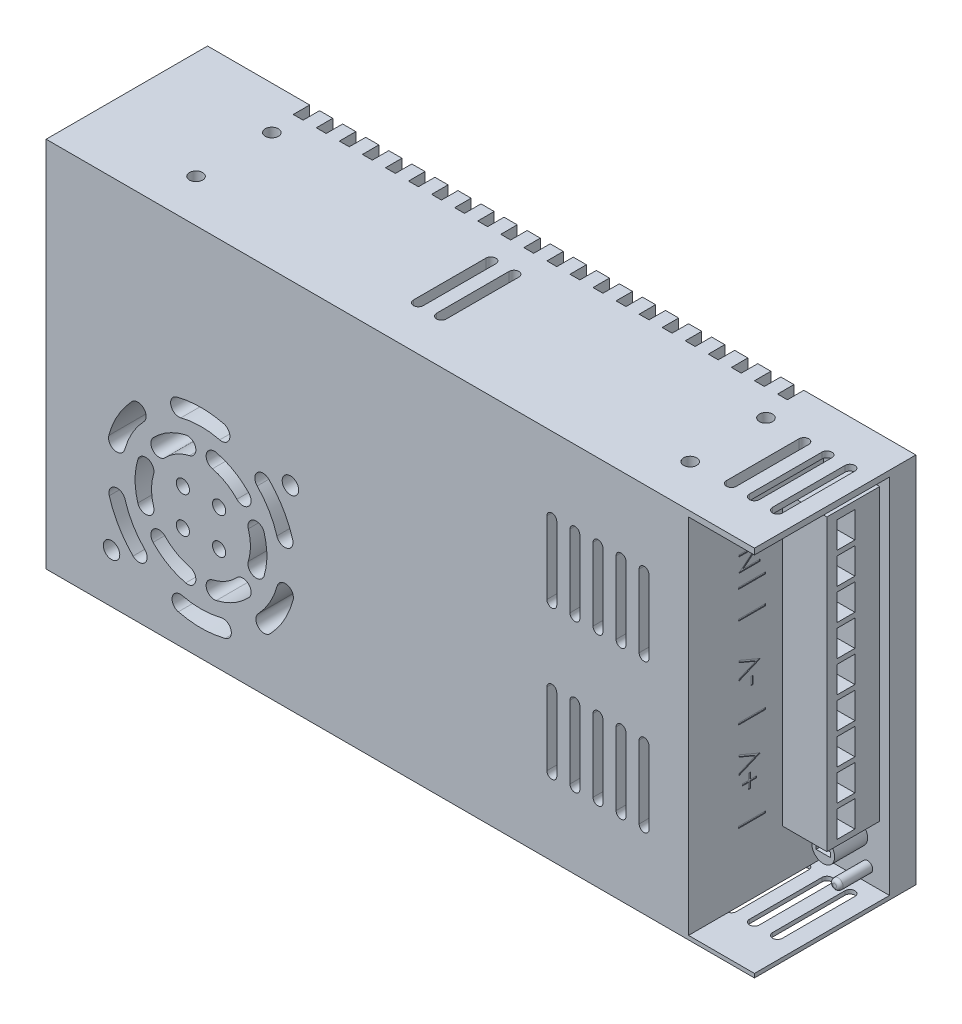
SolidWorks part; units mm, degrees
material "5454-H111"
ref_plane "Front" through (0, 0, 0) normal (0, 0, 1) x (1, 0, 0)
ref_plane "Top" through (0, 0, 0) normal (0, 1, 0) x (1, 0, 0)
ref_plane "Right" through (0, 0, 0) normal (1, 0, 0) x (0, 0, -1)
sketch "Sketch1" plane through (0, 0, 0) normal (0, 0, 1) x (1, 0, 0)
  line L1 (107.5, -56.5) -> (-107.5, -56.5)
  line L2 (107.5, -56.5) -> (107.5, 56.5)
  line L3 (107.5, 56.5) -> (-107.5, 56.5)
  line L4 (-107.5, -56.5) -> (-107.5, 56.5)
  line L5 (107.5, -56.5) -> (-107.5, 56.5) construction
  line L6 (107.5, 56.5) -> (-107.5, -56.5) construction
  point P0 (0, 0)
  dimension "D1" = 113
  dimension "D2" = 215
extrude "Extrude1" add sketch "Sketch1" along normal blind 49
sketch "Sketch2" plane through (0, 0, 49) normal (0, 0, 1) x (1, 0, 0)
  line L0 (107.5, -56.5) -> (107.5, 56.5) construction
  line L1 (107.5, 54.7) -> (87.5, 54.7)
  line L2 (107.5, 54.7) -> (107.5, -55.3)
  line L3 (107.5, -55.3) -> (87.5, -55.3)
  line L4 (87.5, 54.7) -> (87.5, -55.3)
  line L5 (-107.5, -56.5) -> (107.5, -56.5) construction
  dimension "D1" = 20
  dimension "D2" = 110
  dimension "D3" = 1.2
extrude "Extrude2" cut sketch "Sketch2" against normal blind 41
sketch "Sketch3" plane through (0, 0, 49) normal (0, 0, 1) x (1, 0, 0)
  line L0 (75.5, 33.5) -> (75.5, 11.5)
  line L1 (72.5, 33.5) -> (72.5, 11.5)
  line L2 (107.5, 56.5) -> (-107.5, 56.5) construction
  line L3 (87.5, 54.7) -> (87.5, -55.3) construction
  line L4 (65.5, 33.5) -> (65.5, 11.5)
  line L5 (68.5, 33.5) -> (68.5, 11.5)
  line L6 (58.5, 33.5) -> (58.5, 11.5)
  line L7 (61.5, 33.5) -> (61.5, 11.5)
  line L8 (51.5, 33.5) -> (51.5, 11.5)
  line L9 (54.5, 33.5) -> (54.5, 11.5)
  line L10 (44.5, 33.5) -> (44.5, 11.5)
  line L11 (47.5, 33.5) -> (47.5, 11.5)
  line L12 (65.5, -11.5) -> (65.5, -33.5)
  line L13 (68.5, -11.5) -> (68.5, -33.5)
  line L14 (58.5, -11.5) -> (58.5, -33.5)
  line L15 (61.5, -11.5) -> (61.5, -33.5)
  line L16 (51.5, -11.5) -> (51.5, -33.5)
  line L17 (54.5, -11.5) -> (54.5, -33.5)
  line L18 (44.5, -11.5) -> (44.5, -33.5)
  line L19 (47.5, -11.5) -> (47.5, -33.5)
  line L20 (72.5, -11.5) -> (72.5, -33.5)
  line L21 (75.5, -11.5) -> (75.5, -33.5)
  line L22 (-107.5, -56.5) -> (107.5, -56.5) construction
  line L24 (-107.5, 56.5) -> (-107.5, -56.5) construction
  line L25 (-89.5, -19.5) -> (-31.5, -19.5) construction
  line L26 (-55, -25) -> (-66, -25) construction
  line L27 (-55, -25) -> (-55, -14) construction
  line L28 (-55, -14) -> (-66, -14) construction
  line L29 (-66, -25) -> (-66, -14) construction
  line L30 (-55, -25) -> (-66, -14) construction
  line L31 (-55, -14) -> (-66, -25) construction
  line L32 (-60.5, 9.5) -> (-60.5, -48.5) construction
  line L33 (-87.6525, -41.5849) -> (-33.3475, 2.5849) construction
  arc A0 (72.5, 33.5) -> (75.5, 33.5) centre (74, 33.5) cw
  arc A1 (75.5, 11.5) -> (72.5, 11.5) centre (74, 11.5) cw
  arc A2 (65.5, 33.5) -> (68.5, 33.5) centre (67, 33.5) cw
  arc A3 (68.5, 11.5) -> (65.5, 11.5) centre (67, 11.5) cw
  arc A4 (58.5, 33.5) -> (61.5, 33.5) centre (60, 33.5) cw
  arc A5 (61.5, 11.5) -> (58.5, 11.5) centre (60, 11.5) cw
  arc A6 (51.5, 33.5) -> (54.5, 33.5) centre (53, 33.5) cw
  arc A7 (54.5, 11.5) -> (51.5, 11.5) centre (53, 11.5) cw
  arc A8 (44.5, 33.5) -> (47.5, 33.5) centre (46, 33.5) cw
  arc A9 (47.5, 11.5) -> (44.5, 11.5) centre (46, 11.5) cw
  arc A10 (65.5, -11.5) -> (68.5, -11.5) centre (67, -11.5) cw
  arc A11 (68.5, -33.5) -> (65.5, -33.5) centre (67, -33.5) cw
  arc A12 (58.5, -11.5) -> (61.5, -11.5) centre (60, -11.5) cw
  arc A13 (61.5, -33.5) -> (58.5, -33.5) centre (60, -33.5) cw
  arc A14 (51.5, -11.5) -> (54.5, -11.5) centre (53, -11.5) cw
  arc A15 (54.5, -33.5) -> (51.5, -33.5) centre (53, -33.5) cw
  arc A16 (44.5, -11.5) -> (47.5, -11.5) centre (46, -11.5) cw
  arc A17 (47.5, -33.5) -> (44.5, -33.5) centre (46, -33.5) cw
  arc A18 (72.5, -11.5) -> (75.5, -11.5) centre (74, -11.5) cw
  arc A19 (75.5, -33.5) -> (72.5, -33.5) centre (74, -33.5) cw
  arc A20 (-88.3363, -27.6327) -> (-81.1191, -39.8925) centre (-60.5, -19.5) ccw
  arc A21 (-79.6663, -13.7857) -> (-79.6663, -25.2143) centre (-60.5, -19.5) ccw
  arc A22 (-83.5369, -26.2305) -> (-77.5641, -36.3766) centre (-60.5, -19.5) ccw
  arc A23 (-74.8747, -15.2143) -> (-74.8747, -23.7857) centre (-60.5, -19.5) ccw
  circle A24 centre (-66, -14) radius 2
  circle A25 centre (-55, -14) radius 2
  circle A26 centre (-66, -25) radius 2
  circle A27 centre (-55, -25) radius 2
  arc A28 (-74.8747, -15.2143) -> (-79.6663, -13.7857) centre (-77.2705, -14.5) ccw
  arc A29 (-79.6663, -25.2143) -> (-74.8747, -23.7857) centre (-77.2705, -24.5) ccw
  arc A30 (-63.9758, -4.9083) -> (-65.1344, -0.0444) centre (-64.5551, -2.4763) ccw
  arc A31 (-79.6663, -13.7857) -> (-79.6663, -25.2143) centre (-60.5, -19.5) ccw
  arc A32 (-75.0319, -5.7586) -> (-71.3989, -9.194) centre (-73.2154, -7.4763) ccw
  arc A33 (-74.8747, -15.2143) -> (-74.8747, -23.7857) centre (-60.5, -19.5) ccw
  arc A34 (-49.6011, -9.194) -> (-45.9681, -5.7586) centre (-47.7846, -7.4763) ccw
  arc A35 (-79.6663, -13.7857) -> (-79.6663, -25.2143) centre (-60.5, -19.5) ccw
  arc A36 (-55.8656, -0.0444) -> (-57.0242, -4.9083) centre (-56.4449, -2.4763) ccw
  arc A37 (-74.8747, -15.2143) -> (-74.8747, -23.7857) centre (-60.5, -19.5) ccw
  arc A38 (-46.1253, -23.7857) -> (-41.3337, -25.2143) centre (-43.7295, -24.5) ccw
  arc A39 (-65.1344, -0.0444) -> (-75.0319, -5.7586) centre (-60.5, -19.5) ccw
  arc A40 (-41.3337, -13.7857) -> (-46.1253, -15.2143) centre (-43.7295, -14.5) ccw
  arc A41 (-74.8747, -15.2143) -> (-74.8747, -23.7857) centre (-60.5, -19.5) ccw
  arc A42 (-57.0242, -34.0917) -> (-55.8656, -38.9556) centre (-56.4449, -36.5237) ccw
  arc A43 (-65.1344, -0.0444) -> (-75.0319, -5.7586) centre (-60.5, -19.5) ccw
  arc A44 (-45.9681, -33.2414) -> (-49.6011, -29.806) centre (-47.7846, -31.5237) ccw
  arc A45 (-74.8747, -15.2143) -> (-74.8747, -23.7857) centre (-60.5, -19.5) ccw
  arc A46 (-71.3989, -29.806) -> (-75.0319, -33.2414) centre (-73.2154, -31.5237) ccw
  arc A47 (-79.6663, -13.7857) -> (-79.6663, -25.2143) centre (-60.5, -19.5) ccw
  arc A48 (-65.1344, -38.9556) -> (-63.9758, -34.0917) centre (-64.5551, -36.5237) ccw
  arc A49 (-74.8747, -15.2143) -> (-74.8747, -23.7857) centre (-60.5, -19.5) ccw
  arc A50 (-63.9758, -4.9083) -> (-71.3989, -9.194) centre (-60.5, -19.5) ccw
  arc A51 (-63.9758, -4.9083) -> (-71.3989, -9.194) centre (-60.5, -19.5) ccw
  arc A52 (-63.9758, -4.9083) -> (-71.3989, -9.194) centre (-60.5, -19.5) ccw
  arc A53 (-63.9758, -4.9083) -> (-71.3989, -9.194) centre (-60.5, -19.5) ccw
  arc A54 (-63.9758, -4.9083) -> (-71.4703, -9.27) centre (-60.5, -19.5) ccw
  arc A55 (-63.9758, -4.9083) -> (-71.4703, -9.27) centre (-60.5, -19.5) ccw
  arc A56 (-65.1344, -0.0444) -> (-75.0319, -5.7586) centre (-60.5, -19.5) ccw
  arc A57 (-65.1344, -0.0444) -> (-75.0319, -5.7586) centre (-60.5, -19.5) ccw
  arc A58 (-65.1344, -0.0444) -> (-75.0319, -5.7586) centre (-60.5, -19.5) ccw
  arc A59 (-79.6663, -13.7857) -> (-79.6663, -25.2143) centre (-60.5, -19.5) ccw
  arc A60 (-79.6663, -13.7857) -> (-79.6663, -25.2143) centre (-60.5, -19.5) ccw
  arc A61 (-65.1344, -0.0444) -> (-75.0319, -5.7586) centre (-60.5, -19.5) ccw
  arc A62 (-45.9681, -5.7586) -> (-55.8656, -0.0444) centre (-60.5, -19.5) ccw
  arc A63 (-45.9681, -5.7586) -> (-55.8656, -0.0444) centre (-60.5, -19.5) ccw
  arc A64 (-45.9681, -5.7586) -> (-55.8656, -0.0444) centre (-60.5, -19.5) ccw
  arc A65 (-45.9681, -5.7586) -> (-55.8656, -0.0444) centre (-60.5, -19.5) ccw
  arc A66 (-45.9681, -5.7586) -> (-55.8656, -0.0444) centre (-60.5, -19.5) ccw
  arc A67 (-45.9681, -5.7586) -> (-55.8656, -0.0444) centre (-60.5, -19.5) ccw
  arc A68 (-49.6011, -9.194) -> (-57.0242, -4.9083) centre (-60.5, -19.5) ccw
  arc A69 (-49.6011, -9.194) -> (-57.0242, -4.9083) centre (-60.5, -19.5) ccw
  arc A70 (-49.6011, -9.194) -> (-57.0242, -4.9083) centre (-60.5, -19.5) ccw
  arc A71 (-49.6011, -9.194) -> (-57.0242, -4.9083) centre (-60.5, -19.5) ccw
  arc A72 (-49.6011, -9.194) -> (-57.0242, -4.9083) centre (-60.5, -19.5) ccw
  arc A73 (-49.6011, -9.194) -> (-57.0242, -4.9083) centre (-60.5, -19.5) ccw
  arc A74 (-46.1253, -23.7857) -> (-46.1253, -15.2143) centre (-60.5, -19.5) ccw
  arc A75 (-46.1253, -23.7857) -> (-46.1253, -15.2143) centre (-60.5, -19.5) ccw
  arc A76 (-46.1253, -23.7857) -> (-46.1253, -15.2143) centre (-60.5, -19.5) ccw
  arc A77 (-46.1253, -23.7857) -> (-46.1253, -15.2143) centre (-60.5, -19.5) ccw
  arc A78 (-46.1253, -23.7857) -> (-46.1253, -15.2143) centre (-60.5, -19.5) ccw
  arc A79 (-46.1253, -23.7857) -> (-46.1253, -15.2143) centre (-60.5, -19.5) ccw
  arc A80 (-41.3337, -25.2143) -> (-41.3337, -13.7857) centre (-60.5, -19.5) ccw
  arc A81 (-41.3337, -25.2143) -> (-41.3337, -13.7857) centre (-60.5, -19.5) ccw
  arc A82 (-41.3337, -25.2143) -> (-41.3337, -13.7857) centre (-60.5, -19.5) ccw
  arc A83 (-41.3337, -25.2143) -> (-41.3337, -13.7857) centre (-60.5, -19.5) ccw
  arc A84 (-41.3337, -25.2143) -> (-41.3337, -13.7857) centre (-60.5, -19.5) ccw
  arc A85 (-41.3337, -25.2143) -> (-41.3337, -13.7857) centre (-60.5, -19.5) ccw
  arc A86 (-71.3989, -29.806) -> (-63.9758, -34.0917) centre (-60.5, -19.5) ccw
  arc A87 (-71.3989, -29.806) -> (-63.9758, -34.0917) centre (-60.5, -19.5) ccw
  arc A88 (-71.3989, -29.806) -> (-63.9758, -34.0917) centre (-60.5, -19.5) ccw
  arc A89 (-71.3989, -29.806) -> (-63.9758, -34.0917) centre (-60.5, -19.5) ccw
  arc A90 (-71.3989, -29.806) -> (-63.9758, -34.0917) centre (-60.5, -19.5) ccw
  arc A91 (-71.3989, -29.806) -> (-63.9758, -34.0917) centre (-60.5, -19.5) ccw
  arc A92 (-75.0319, -33.2414) -> (-65.1344, -38.9556) centre (-60.5, -19.5) ccw
  arc A93 (-75.0319, -33.2414) -> (-65.1344, -38.9556) centre (-60.5, -19.5) ccw
  arc A94 (-75.0319, -33.2414) -> (-65.1344, -38.9556) centre (-60.5, -19.5) ccw
  arc A95 (-75.0319, -33.2414) -> (-65.1344, -38.9556) centre (-60.5, -19.5) ccw
  arc A96 (-75.0319, -33.2414) -> (-65.1344, -38.9556) centre (-60.5, -19.5) ccw
  arc A97 (-75.0319, -33.2414) -> (-65.1344, -38.9556) centre (-60.5, -19.5) ccw
  arc A98 (-55.8656, -38.9556) -> (-45.9681, -33.2414) centre (-60.5, -19.5) ccw
  arc A99 (-55.8656, -38.9556) -> (-45.9681, -33.2414) centre (-60.5, -19.5) ccw
  arc A100 (-55.8656, -38.9556) -> (-45.9681, -33.2414) centre (-60.5, -19.5) ccw
  arc A101 (-55.8656, -38.9556) -> (-45.9681, -33.2414) centre (-60.5, -19.5) ccw
  arc A102 (-55.8656, -38.9556) -> (-45.9681, -33.2414) centre (-60.5, -19.5) ccw
  arc A103 (-55.8656, -38.9556) -> (-45.9681, -33.2414) centre (-60.5, -19.5) ccw
  arc A104 (-57.0242, -34.0917) -> (-49.6011, -29.806) centre (-60.5, -19.5) ccw
  arc A105 (-57.0242, -34.0917) -> (-49.6011, -29.806) centre (-60.5, -19.5) ccw
  arc A106 (-57.0242, -34.0917) -> (-49.6011, -29.806) centre (-60.5, -19.5) ccw
  arc A107 (-57.0242, -34.0917) -> (-49.6011, -29.806) centre (-60.5, -19.5) ccw
  arc A108 (-57.0242, -34.0917) -> (-49.6011, -29.806) centre (-60.5, -19.5) ccw
  arc A109 (-57.0242, -34.0917) -> (-49.6011, -29.806) centre (-60.5, -19.5) ccw
  arc A110 (-88.47, -11.8396) -> (-83.6476, -13.1604) centre (-86.0588, -12.5) ccw
  arc A112 (-77.8473, -2.9147) -> (-81.4613, 0.5406) centre (-79.6543, -1.1871) ccw
  arc A113 (-67.8509, 8.5529) -> (-66.5835, 3.7162) centre (-67.2172, 6.1345) ccw
  arc A114 (-54.8103, 3.8158) -> (-53.625, 8.6733) centre (-54.2177, 6.2446) ccw
  arc A115 (-39.8809, 0.8925) -> (-43.4359, -2.6234) centre (-41.6584, -0.8655) ccw
  arc A116 (-37.4631, -12.7695) -> (-32.6637, -11.3673) centre (-35.0634, -12.0684) ccw
  arc A117 (-32.53, -27.1604) -> (-37.3524, -25.8396) centre (-34.9412, -26.5) ccw
  arc A118 (-43.1527, -36.0853) -> (-39.5387, -39.5406) centre (-41.3457, -37.8129) ccw
  arc A119 (-53.1491, -47.5529) -> (-54.4165, -42.7162) centre (-53.7828, -45.1345) ccw
  arc A120 (-66.1897, -42.8158) -> (-67.375, -47.6733) centre (-66.7823, -45.2446) ccw
  arc A121 (-81.1191, -39.8925) -> (-77.5641, -36.3766) centre (-79.3416, -38.1345) ccw
  arc A122 (-83.5369, -26.2305) -> (-88.3363, -27.6327) centre (-85.9366, -26.9316) ccw
  arc A123 (-66.1897, -42.8158) -> (-54.4165, -42.7162) centre (-60.5, -19.5) ccw
  arc A124 (-67.375, -47.6733) -> (-53.1491, -47.5529) centre (-60.5, -19.5) ccw
  arc A125 (-39.5387, -39.5406) -> (-32.53, -27.1604) centre (-60.5, -19.5) ccw
  arc A126 (-43.1527, -36.0853) -> (-37.3524, -25.8396) centre (-60.5, -19.5) ccw
  arc A127 (-32.6637, -11.3673) -> (-39.8809, 0.8925) centre (-60.5, -19.5) ccw
  arc A128 (-37.4631, -12.7695) -> (-43.4359, -2.6234) centre (-60.5, -19.5) ccw
  arc A129 (-53.625, 8.6733) -> (-67.8509, 8.5529) centre (-60.5, -19.5) ccw
  arc A130 (-54.8103, 3.8158) -> (-66.5835, 3.7162) centre (-60.5, -19.5) ccw
  arc A131 (-77.8473, -2.9147) -> (-83.6476, -13.1604) centre (-60.5, -19.5) ccw
  arc A132 (-81.4613, 0.5406) -> (-88.47, -11.8396) centre (-60.5, -19.5) ccw
  circle A133 centre (-87.6525, -41.5849) radius 2.5
  circle A134 centre (-33.3475, 2.5849) radius 2.5
  point P133 (-60.5, -19.5)
  point P159 (-60.5, -19.5)
  dimension "D2" = 25
  dimension "D3" = 21.5
  dimension "D7" = 58
  dimension "D8" = 8
  dimension "D9" = 27
  dimension "D10" = 40
  dimension "D11" = 5
  dimension "D12" = 5
  dimension "D15" = 4
  dimension "D16" = 7.5
  dimension "D19" = 6
  dimension "D20" = 4.5
  dimension "D21" = 18
  dimension "D22" = 5
  dimension "D23" = 5
  dimension "D1" = 3
  dimension "D4" = 12
  dimension "D13" = 11
  dimension "D14" = 11
  dimension "D17" = 7.5
  dimension "D24" = 35
  dimension "D25" = 35
  dimension "D5" = 5
  dimension "D6" = 2
  dimension "D18" = 6
extrude "Extrude3" cut sketch "Sketch3" against normal blind 30 contours A126 A118 A125 A117 | A104 A42 A98 A44 | A120 A124 A119 A123 | A46 A92 A48 A86 | A22 A122 A20 A121 | A133 | A112 A132 A110 A131 | A21 A29 A23 A28 | A27 | A26 | A24 | A25 | A68 A34 A62 A36 | A50 A30 A39 A32 | A130 A114 A129 A113 | A128 A116 A127 A115 | A38 A80 A40 A74 | A134 | A15 L17 A14 L16 | A7 L9 A6 L8 | L19 A17 L18 A16 | L15 A13 L14 A12 | L12 A11 L13 A10 | L21 A19 L20 A18 | L0 A1 L1 A0 | L5 A3 L4 A2 | L7 A5 L6 A4 | L10 A9 L11 A8
sketch "Sketch4" plane through (0, 0, 0) normal (0, 0, -1) x (-1, 0, 0)
  line L0 (-107.5, 56.5) -> (107.5, 56.5) construction
  line L1 (-73.5, 56.5) -> (-70.5, 56.5)
  line L2 (-73.5, 56.5) -> (-73.5, 36)
  line L4 (-70.5, 56.5) -> (-70.5, 36)
  line L5 (-107.5, -56.5) -> (-107.5, 56.5) construction
  line L6 (-63.5, 56.5) -> (-63.5, 36)
  line L7 (-66.5, 56.5) -> (-66.5, 36)
  line L8 (-56.5, 56.5) -> (-56.5, 36)
  line L9 (-59.5, 56.5) -> (-59.5, 36)
  line L10 (-49.5, 56.5) -> (-49.5, 36)
  line L11 (-52.5, 56.5) -> (-52.5, 36)
  line L12 (-42.5, 56.5) -> (-42.5, 36)
  line L13 (-45.5, 56.5) -> (-45.5, 36)
  line L14 (-35.5, 56.5) -> (-35.5, 36)
  line L15 (-38.5, 56.5) -> (-38.5, 36)
  line L16 (-28.5, 56.5) -> (-28.5, 36)
  line L17 (-31.5, 56.5) -> (-31.5, 36)
  line L18 (-21.5, 56.5) -> (-21.5, 36)
  line L19 (-24.5, 56.5) -> (-24.5, 36)
  line L20 (-14.5, 56.5) -> (-14.5, 36)
  line L21 (-17.5, 56.5) -> (-17.5, 36)
  line L22 (-7.5, 56.5) -> (-7.5, 36)
  line L23 (-10.5, 56.5) -> (-10.5, 36)
  line L24 (-0.5, 56.5) -> (-0.5, 36)
  line L25 (-3.5, 56.5) -> (-3.5, 36)
  line L26 (6.5, 56.5) -> (6.5, 36)
  line L27 (3.5, 56.5) -> (3.5, 36)
  line L28 (13.5, 56.5) -> (13.5, 36)
  line L29 (10.5, 56.5) -> (10.5, 36)
  line L30 (20.5, 56.5) -> (20.5, 36)
  line L31 (17.5, 56.5) -> (17.5, 36)
  line L32 (27.5, 56.5) -> (27.5, 36)
  line L33 (24.5, 56.5) -> (24.5, 36)
  line L34 (34.5, 56.5) -> (34.5, 36)
  line L35 (31.5, 56.5) -> (31.5, 36)
  line L36 (41.5, 56.5) -> (41.5, 36)
  line L37 (38.5, 56.5) -> (38.5, 36)
  line L38 (48.5, 56.5) -> (48.5, 36)
  line L39 (45.5, 56.5) -> (45.5, 36)
  line L40 (55.5, 56.5) -> (55.5, 36)
  line L41 (52.5, 56.5) -> (52.5, 36)
  line L42 (62.5, 56.5) -> (62.5, 36)
  line L43 (59.5, 56.5) -> (59.5, 36)
  line L44 (69.5, 56.5) -> (69.5, 36)
  line L45 (66.5, 56.5) -> (66.5, 36)
  line L46 (76.5, 56.5) -> (76.5, 36)
  line L47 (73.5, 56.5) -> (73.5, 36)
  line L48 (-107.5, 0) -> (107.5, 0) construction
  line L49 (107.5, 56.5) -> (107.5, -56.5) construction
  line L50 (73.5, -56.5) -> (73.5, -36)
  line L51 (76.5, -56.5) -> (76.5, -36)
  line L52 (66.5, -56.5) -> (66.5, -36)
  line L53 (69.5, -56.5) -> (69.5, -36)
  line L54 (59.5, -56.5) -> (59.5, -36)
  line L55 (62.5, -56.5) -> (62.5, -36)
  line L56 (52.5, -56.5) -> (52.5, -36)
  line L57 (55.5, -56.5) -> (55.5, -36)
  line L58 (45.5, -56.5) -> (45.5, -36)
  line L59 (48.5, -56.5) -> (48.5, -36)
  line L60 (38.5, -56.5) -> (38.5, -36)
  line L61 (41.5, -56.5) -> (41.5, -36)
  line L62 (31.5, -56.5) -> (31.5, -36)
  line L63 (34.5, -56.5) -> (34.5, -36)
  line L64 (24.5, -56.5) -> (24.5, -36)
  line L65 (27.5, -56.5) -> (27.5, -36)
  line L66 (17.5, -56.5) -> (17.5, -36)
  line L67 (20.5, -56.5) -> (20.5, -36)
  line L68 (10.5, -56.5) -> (10.5, -36)
  line L69 (13.5, -56.5) -> (13.5, -36)
  line L70 (3.5, -56.5) -> (3.5, -36)
  line L71 (6.5, -56.5) -> (6.5, -36)
  line L72 (-3.5, -56.5) -> (-3.5, -36)
  line L73 (-0.5, -56.5) -> (-0.5, -36)
  line L74 (-10.5, -56.5) -> (-10.5, -36)
  line L75 (-7.5, -56.5) -> (-7.5, -36)
  line L76 (-17.5, -56.5) -> (-17.5, -36)
  line L77 (-14.5, -56.5) -> (-14.5, -36)
  line L78 (-24.5, -56.5) -> (-24.5, -36)
  line L79 (-21.5, -56.5) -> (-21.5, -36)
  line L80 (-31.5, -56.5) -> (-31.5, -36)
  line L81 (-28.5, -56.5) -> (-28.5, -36)
  line L82 (-38.5, -56.5) -> (-38.5, -36)
  line L83 (-35.5, -56.5) -> (-35.5, -36)
  line L84 (-45.5, -56.5) -> (-45.5, -36)
  line L85 (-42.5, -56.5) -> (-42.5, -36)
  line L86 (-52.5, -56.5) -> (-52.5, -36)
  line L87 (-49.5, -56.5) -> (-49.5, -36)
  line L88 (-59.5, -56.5) -> (-59.5, -36)
  line L89 (-56.5, -56.5) -> (-56.5, -36)
  line L90 (-66.5, -56.5) -> (-66.5, -36)
  line L91 (-63.5, -56.5) -> (-63.5, -36)
  line L92 (-70.5, -56.5) -> (-70.5, -36)
  line L93 (-73.5, -56.5) -> (-73.5, -36)
  line L94 (-73.5, -56.5) -> (-70.5, -56.5)
  line L95 (-66.5, -56.5) -> (-63.5, -56.5)
  line L96 (-59.5, -56.5) -> (-56.5, -56.5)
  line L97 (-52.5, -56.5) -> (-49.5, -56.5)
  line L98 (-45.5, -56.5) -> (-42.5, -56.5)
  line L99 (-38.5, -56.5) -> (-35.5, -56.5)
  line L100 (-31.5, -56.5) -> (-28.5, -56.5)
  line L101 (-24.5, -56.5) -> (-21.5, -56.5)
  line L102 (-17.5, -56.5) -> (-14.5, -56.5)
  line L103 (-10.5, -56.5) -> (-7.5, -56.5)
  line L104 (-3.5, -56.5) -> (-0.5, -56.5)
  line L105 (3.5, -56.5) -> (6.5, -56.5)
  line L106 (10.5, -56.5) -> (13.5, -56.5)
  line L107 (17.5, -56.5) -> (20.5, -56.5)
  line L108 (24.5, -56.5) -> (27.5, -56.5)
  line L109 (31.5, -56.5) -> (34.5, -56.5)
  line L110 (38.5, -56.5) -> (41.5, -56.5)
  line L111 (45.5, -56.5) -> (48.5, -56.5)
  line L112 (52.5, -56.5) -> (55.5, -56.5)
  line L113 (59.5, -56.5) -> (62.5, -56.5)
  line L114 (66.5, -56.5) -> (69.5, -56.5)
  line L115 (73.5, -56.5) -> (76.5, -56.5)
  line L116 (107.5, -56.5) -> (-107.5, -56.5) construction
  line L117 (-66.5, 56.5) -> (-63.5, 56.5)
  line L118 (-59.5, 56.5) -> (-56.5, 56.5)
  line L119 (-52.5, 56.5) -> (-49.5, 56.5)
  line L120 (-45.5, 56.5) -> (-42.5, 56.5)
  line L121 (-38.5, 56.5) -> (-35.5, 56.5)
  line L122 (-31.5, 56.5) -> (-28.5, 56.5)
  line L123 (-24.5, 56.5) -> (-21.5, 56.5)
  line L124 (-17.5, 56.5) -> (-14.5, 56.5)
  line L125 (-10.5, 56.5) -> (-7.5, 56.5)
  line L126 (-3.5, 56.5) -> (-0.5, 56.5)
  line L127 (3.5, 56.5) -> (6.5, 56.5)
  line L128 (10.5, 56.5) -> (13.5, 56.5)
  line L129 (17.5, 56.5) -> (20.5, 56.5)
  line L130 (24.5, 56.5) -> (27.5, 56.5)
  line L131 (31.5, 56.5) -> (34.5, 56.5)
  line L132 (38.5, 56.5) -> (41.5, 56.5)
  line L133 (45.5, 56.5) -> (48.5, 56.5)
  line L134 (52.5, 56.5) -> (55.5, 56.5)
  line L135 (59.5, 56.5) -> (62.5, 56.5)
  line L136 (66.5, 56.5) -> (69.5, 56.5)
  line L137 (73.5, 56.5) -> (76.5, 56.5)
  arc A0 (-70.5, 36) -> (-73.5, 36) centre (-72, 36) cw
  arc A1 (-63.5, 36) -> (-66.5, 36) centre (-65, 36) cw
  arc A2 (-56.5, 36) -> (-59.5, 36) centre (-58, 36) cw
  arc A3 (-49.5, 36) -> (-52.5, 36) centre (-51, 36) cw
  arc A4 (-42.5, 36) -> (-45.5, 36) centre (-44, 36) cw
  arc A5 (-35.5, 36) -> (-38.5, 36) centre (-37, 36) cw
  arc A6 (-28.5, 36) -> (-31.5, 36) centre (-30, 36) cw
  arc A7 (-21.5, 36) -> (-24.5, 36) centre (-23, 36) cw
  arc A8 (-14.5, 36) -> (-17.5, 36) centre (-16, 36) cw
  arc A9 (-7.5, 36) -> (-10.5, 36) centre (-9, 36) cw
  arc A10 (-0.5, 36) -> (-3.5, 36) centre (-2, 36) cw
  arc A11 (6.5, 36) -> (3.5, 36) centre (5, 36) cw
  arc A12 (13.5, 36) -> (10.5, 36) centre (12, 36) cw
  arc A13 (20.5, 36) -> (17.5, 36) centre (19, 36) cw
  arc A14 (27.5, 36) -> (24.5, 36) centre (26, 36) cw
  arc A15 (34.5, 36) -> (31.5, 36) centre (33, 36) cw
  arc A16 (41.5, 36) -> (38.5, 36) centre (40, 36) cw
  arc A17 (48.5, 36) -> (45.5, 36) centre (47, 36) cw
  arc A18 (55.5, 36) -> (52.5, 36) centre (54, 36) cw
  arc A19 (62.5, 36) -> (59.5, 36) centre (61, 36) cw
  arc A20 (69.5, 36) -> (66.5, 36) centre (68, 36) cw
  arc A21 (76.5, 36) -> (73.5, 36) centre (75, 36) cw
  arc A22 (76.5, -36) -> (73.5, -36) centre (75, -36) ccw
  arc A23 (69.5, -36) -> (66.5, -36) centre (68, -36) ccw
  arc A24 (62.5, -36) -> (59.5, -36) centre (61, -36) ccw
  arc A25 (55.5, -36) -> (52.5, -36) centre (54, -36) ccw
  arc A26 (48.5, -36) -> (45.5, -36) centre (47, -36) ccw
  arc A27 (41.5, -36) -> (38.5, -36) centre (40, -36) ccw
  arc A28 (34.5, -36) -> (31.5, -36) centre (33, -36) ccw
  arc A29 (27.5, -36) -> (24.5, -36) centre (26, -36) ccw
  arc A30 (20.5, -36) -> (17.5, -36) centre (19, -36) ccw
  arc A31 (13.5, -36) -> (10.5, -36) centre (12, -36) ccw
  arc A32 (6.5, -36) -> (3.5, -36) centre (5, -36) ccw
  arc A33 (-0.5, -36) -> (-3.5, -36) centre (-2, -36) ccw
  arc A34 (-7.5, -36) -> (-10.5, -36) centre (-9, -36) ccw
  arc A35 (-14.5, -36) -> (-17.5, -36) centre (-16, -36) ccw
  arc A36 (-21.5, -36) -> (-24.5, -36) centre (-23, -36) ccw
  arc A37 (-28.5, -36) -> (-31.5, -36) centre (-30, -36) ccw
  arc A38 (-35.5, -36) -> (-38.5, -36) centre (-37, -36) ccw
  arc A39 (-42.5, -36) -> (-45.5, -36) centre (-44, -36) ccw
  arc A40 (-49.5, -36) -> (-52.5, -36) centre (-51, -36) ccw
  arc A41 (-56.5, -36) -> (-59.5, -36) centre (-58, -36) ccw
  arc A42 (-63.5, -36) -> (-66.5, -36) centre (-65, -36) ccw
  arc A43 (-70.5, -36) -> (-73.5, -36) centre (-72, -36) ccw
  dimension "D3" = 22
  dimension "D1" = 34
  dimension "D2" = 3
  dimension "D4" = 22
extrude "Extrude4" cut sketch "Sketch4" against normal blind 5
sketch "Sketch5" plane through (0, 0, 0) normal (0, 0, -1) x (-1, 0, 0)
  line L0 (0, 29.4545) -> (0, -29.0292) construction
  line L1 (-99.316, 0) -> (99.316, 0) construction
  line L2 (-75, 27.7417) -> (-75, -30.742) construction
  line L3 (75, 27.7417) -> (75, -30.742) construction
  circle A0 centre (-75, 25) radius 2
  circle A1 centre (-75, -25) radius 2
  circle A2 centre (75, 25) radius 2
  circle A3 centre (75, -25) radius 2
  dimension "D1" = 4
  dimension "D2" = 50
  dimension "D3" = 50
  dimension "D4" = 25
  dimension "D5" = 25
  dimension "D6" = 150
  dimension "D7" = 75
extrude "Extrude5" cut sketch "Sketch5" against normal blind 5
sketch "Sketch6" plane through (0, 0, 8) normal (0, 0, 1) x (1, 0, 0)
  line L0 (107.5, 54.7) -> (87.5, 54.7) construction
  line L1 (91.0117, 50.7) -> (104.5, 50.7)
  line L2 (91.0117, 50.7) -> (91.0117, -37.3)
  line L3 (91.0117, -37.3) -> (104.5, -37.3)
  line L4 (104.5, 50.7) -> (104.5, -37.3)
  line L5 (107.5, -55.3) -> (107.5, 54.7) construction
  dimension "D1" = 88
  dimension "D2" = 4
  dimension "D3" = 3
extrude "Extrude6" add sketch "Sketch6" along normal blind 16
sketch "Sketch7" plane through (0, 0, 8) normal (0, 0, 1) x (1, 0, 0)
  circle A0 centre (97.3937, -43.5319) radius 3.4559
  circle A1 centre (100.8496, -50.9948) radius 1.5592
extrude "Extrude7" add sketch "Sketch7" along normal blind 10
fillet "Fillet1" radius 1 1 edges at (102.4088, -50.9948, 18)
sketch "Sketch8" plane through (0, 0, 18) normal (0, 0, 1) x (1, 0, 0)
  line L1 (95.2283, -42.8812) -> (99.5237, -42.8812)
  line L2 (95.2283, -42.8812) -> (95.2283, -44.3223)
  line L3 (95.2283, -44.3223) -> (99.5237, -44.3223)
  line L4 (99.5237, -42.8812) -> (99.5237, -44.3223)
extrude "Extrude8" cut sketch "Sketch8" against normal blind 5
sketch "Sketch9" plane through (104.5, 0, 0) normal (1, 0, 0) x (0, 0, -1)
  line L0 (-24, -37.3) -> (-8, -37.3) construction
  line L5 (-21, -27.6) -> (-15.5, -27.6)
  line L6 (-21, -27.6) -> (-21, -35.6)
  line L7 (-21, -35.6) -> (-15.5, -35.6)
  line L8 (-15.5, -27.6) -> (-15.5, -35.6)
  line L9 (-24, -37.3) -> (-24, 50.7) construction
  line L10 (-21, -18.1) -> (-15.5, -18.1)
  line L11 (-15.5, -18.1) -> (-15.5, -26.1)
  line L12 (-21, -26.1) -> (-15.5, -26.1)
  line L13 (-21, -18.1) -> (-21, -26.1)
  line L14 (-21, -8.6) -> (-15.5, -8.6)
  line L15 (-15.5, -8.6) -> (-15.5, -16.6)
  line L16 (-21, -16.6) -> (-15.5, -16.6)
  line L17 (-21, -8.6) -> (-21, -16.6)
  line L18 (-21, 0.9) -> (-15.5, 0.9)
  line L19 (-15.5, 0.9) -> (-15.5, -7.1)
  line L20 (-21, -7.1) -> (-15.5, -7.1)
  line L21 (-21, 0.9) -> (-21, -7.1)
  line L22 (-21, 10.4) -> (-15.5, 10.4)
  line L23 (-15.5, 10.4) -> (-15.5, 2.4)
  line L24 (-21, 2.4) -> (-15.5, 2.4)
  line L25 (-21, 10.4) -> (-21, 2.4)
  line L26 (-21, 19.9) -> (-15.5, 19.9)
  line L27 (-15.5, 19.9) -> (-15.5, 11.9)
  line L28 (-21, 11.9) -> (-15.5, 11.9)
  line L29 (-21, 19.9) -> (-21, 11.9)
  line L30 (-21, 29.4) -> (-15.5, 29.4)
  line L31 (-15.5, 29.4) -> (-15.5, 21.4)
  line L32 (-21, 21.4) -> (-15.5, 21.4)
  line L33 (-21, 29.4) -> (-21, 21.4)
  line L34 (-21, 38.9) -> (-15.5, 38.9)
  line L35 (-15.5, 38.9) -> (-15.5, 30.9)
  line L36 (-21, 30.9) -> (-15.5, 30.9)
  line L37 (-21, 38.9) -> (-21, 30.9)
  line L38 (-21, 48.4) -> (-15.5, 48.4)
  line L39 (-15.5, 48.4) -> (-15.5, 40.4)
  line L40 (-21, 40.4) -> (-15.5, 40.4)
  line L41 (-21, 48.4) -> (-21, 40.4)
  dimension "D1" = 8
  dimension "D2" = 1.7
  dimension "D3" = 3
  dimension "D4" = 5.5
  dimension "D5" = 9
extrude "Extrude9" cut sketch "Sketch9" against normal blind 15
sketch "Sketch10" plane through (87.5, 0, 0) normal (1, 0, 0) x (0, 0, -1)
  line L0 (-27.3254, -37.3918) -> (-27.3254, 50.2656) construction
  text T0 "|  +V  |  -V   | |N|L|"
extrude "Extrude10" cut sketch "Sketch10" against normal blind 0.2
sketch "Sketch11" plane through (0, 56.5, 0) normal (0, 1, 0) x (1, 0, 0)
  line L0 (-107.5, -24.5) -> (107.5, -24.5) construction
  line L1 (-107.5, -49) -> (-107.5, 0) construction
  line L2 (107.5, -49) -> (107.5, 0) construction
  line L3 (-75, -13) -> (-75, -36) construction
  line L4 (75, -13) -> (75, -36) construction
  circle A0 centre (-75, -13) radius 2
  circle A1 centre (-75, -36) radius 2
  circle A2 centre (75, -13) radius 2
  circle A3 centre (75, -36) radius 2
  point P14 (0, -24.5)
  dimension "D1" = 4
  dimension "D2" = 23
  dimension "D4" = 23
  dimension "D5" = 11.5
  dimension "D3" = 11.5
  dimension "D6" = 150
  dimension "D7" = 75
extrude "Extrude11" cut sketch "Sketch11" against normal blind 3
sketch "Sketch12" plane through (0, 56.5, 0) normal (0, 1, 0) x (1, 0, 0)
  line L0 (107.5, -49) -> (-107.5, -49) construction
  line L2 (99.5, -13.5) -> (99.5, -35.5)
  line L4 (102.5, -13.5) -> (102.5, -35.5)
  line L5 (107.5, -49) -> (107.5, 0) construction
  line L6 (95.5, -13.5) -> (95.5, -35.5)
  line L7 (92.5, -13.5) -> (92.5, -35.5)
  line L8 (88.5, -13.5) -> (88.5, -35.5)
  line L9 (85.5, -13.5) -> (85.5, -35.5)
  arc A0 (99.5, -13.5) -> (102.5, -13.5) centre (101, -13.5) cw
  arc A1 (102.5, -35.5) -> (99.5, -35.5) centre (101, -35.5) cw
  arc A2 (92.5, -13.5) -> (95.5, -13.5) centre (94, -13.5) cw
  arc A3 (95.5, -35.5) -> (92.5, -35.5) centre (94, -35.5) cw
  arc A4 (85.5, -13.5) -> (88.5, -13.5) centre (87, -13.5) cw
  arc A5 (88.5, -35.5) -> (85.5, -35.5) centre (87, -35.5) cw
  dimension "D2" = 25
  dimension "D3" = 12
  dimension "D1" = 3
  dimension "D4" = 5
  dimension "D5" = 3
extrude "Extrude12" cut sketch "Sketch12" against normal blind 3
sketch "Sketch13" plane through (0, -55.3, 0) normal (0, 1, 0) x (1, 0, 0)
  line L0 (95.5, -35.5) -> (95.5, -13.5) construction
  line L1 (92.5, -13.5) -> (92.5, -35.5) construction
  line L2 (88.5, -35.5) -> (88.5, -13.5) construction
  line L3 (85.5, -13.5) -> (85.5, -35.5) construction
  line L4 (102.5, -35.5) -> (102.5, -13.5) construction
  line L5 (99.5, -13.5) -> (99.5, -35.5) construction
  line L6 (95.5, -35.5) -> (95.5, -13.5)
  line L7 (92.5, -13.5) -> (92.5, -35.5)
  line L8 (88.5, -35.5) -> (88.5, -13.5)
  line L9 (85.5, -13.5) -> (85.5, -35.5)
  line L10 (102.5, -35.5) -> (102.5, -13.5)
  line L11 (99.5, -13.5) -> (99.5, -35.5)
  arc A0 (92.5, -35.5) -> (95.5, -35.5) centre (94, -35.5) ccw construction
  arc A1 (85.5, -35.5) -> (88.5, -35.5) centre (87, -35.5) ccw construction
  arc A2 (88.5, -13.5) -> (85.5, -13.5) centre (87, -13.5) ccw construction
  arc A3 (95.5, -13.5) -> (92.5, -13.5) centre (94, -13.5) ccw construction
  arc A4 (102.5, -13.5) -> (99.5, -13.5) centre (101, -13.5) ccw construction
  arc A5 (99.5, -35.5) -> (102.5, -35.5) centre (101, -35.5) ccw construction
  arc A6 (92.5, -35.5) -> (95.5, -35.5) centre (94, -35.5) ccw
  arc A7 (85.5, -35.5) -> (88.5, -35.5) centre (87, -35.5) ccw
  arc A8 (88.5, -13.5) -> (85.5, -13.5) centre (87, -13.5) ccw
  arc A9 (95.5, -13.5) -> (92.5, -13.5) centre (94, -13.5) ccw
  arc A10 (102.5, -13.5) -> (99.5, -13.5) centre (101, -13.5) ccw
  arc A11 (99.5, -35.5) -> (102.5, -35.5) centre (101, -35.5) ccw
extrude "Extrude13" cut sketch "Sketch13" against normal blind 3
sketch "Sketch14" plane through (0, 56.5, 0) normal (0, 1, 0) x (1, 0, 0)
  line L2 (88.5, -35.5) -> (88.5, -13.5) construction
  line L4 (85.5, -13.5) -> (85.5, -35.5) construction
  line L5 (88.5, -35.5) -> (88.5, -13.5)
  line L6 (85.5, -13.5) -> (85.5, -35.5)
  line L7 (0.5, -35.5) -> (0.5, -13.5)
  line L8 (-2.5, -13.5) -> (-2.5, -35.5)
  line L9 (-6.5, -35.5) -> (-6.5, -13.5)
  line L10 (-9.5, -13.5) -> (-9.5, -35.5)
  arc A0 (87.5, -12.0858) -> (85.5, -13.5) centre (87, -13.5) ccw construction
  arc A2 (85.5, -35.5) -> (88.5, -35.5) centre (87, -35.5) ccw construction
  arc A3 (88.5, -13.5) -> (85.5, -13.5) centre (87, -13.5) ccw construction
  arc A4 (85.5, -35.5) -> (88.5, -35.5) centre (87, -35.5) ccw
  arc A5 (88.5, -13.5) -> (85.5, -13.5) centre (87, -13.5) ccw
  arc A6 (87.5, -12.0858) -> (85.5, -13.5) centre (87, -13.5) ccw
  arc A7 (-2.5, -35.5) -> (0.5, -35.5) centre (-1, -35.5) ccw
  arc A8 (0.5, -13.5) -> (-2.5, -13.5) centre (-1, -13.5) ccw
  arc A9 (-0.5, -12.0858) -> (-2.5, -13.5) centre (-1, -13.5) ccw
  arc A10 (-9.5, -35.5) -> (-6.5, -35.5) centre (-8, -35.5) ccw
  arc A11 (-6.5, -13.5) -> (-9.5, -13.5) centre (-8, -13.5) ccw
  arc A12 (-7.5, -12.0858) -> (-9.5, -13.5) centre (-8, -13.5) ccw
  dimension "D1" = 2
  dimension "D2" = 2
extrude "Extrude14" cut sketch "Sketch14" against normal blind 3 contours L7 A8 L8 A7 | L9 A11 L10 A10
